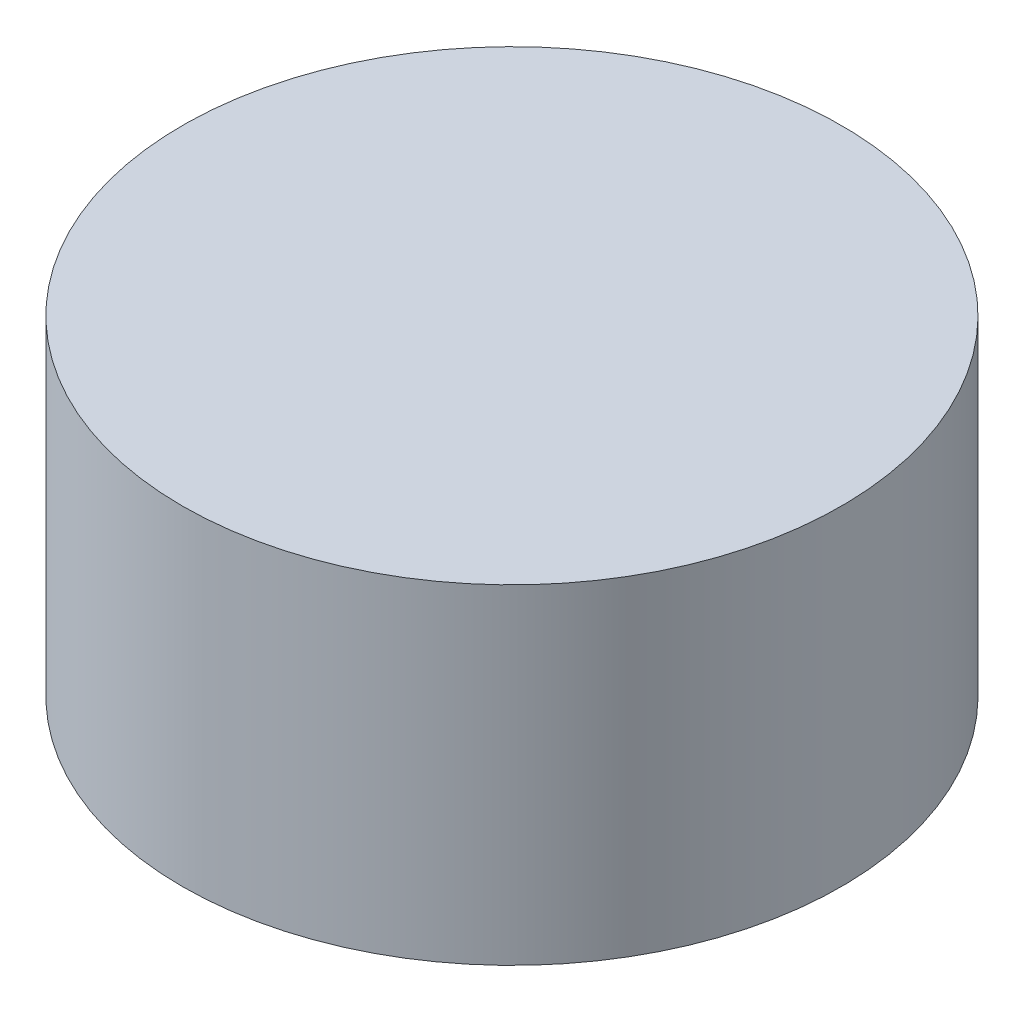
SolidWorks part; units mm, degrees
ref_plane "Front Plane" through (0, 0, 0) normal (0, 0, 1) x (1, 0, 0)
ref_plane "Top Plane" through (0, 0, 0) normal (0, 1, 0) x (1, 0, 0)
ref_plane "Right Plane" through (0, 0, 0) normal (1, 0, 0) x (0, 0, -1)
sketch "Sketch2" plane through (0, 0, 0) normal (0, 1, 0) x (1, 0, 0)
  circle A0 centre (0, 0) radius 20
  dimension "D1" = 40
extrude "Boss-Extrude1" add sketch "Sketch2" along normal blind 20 contours A0
